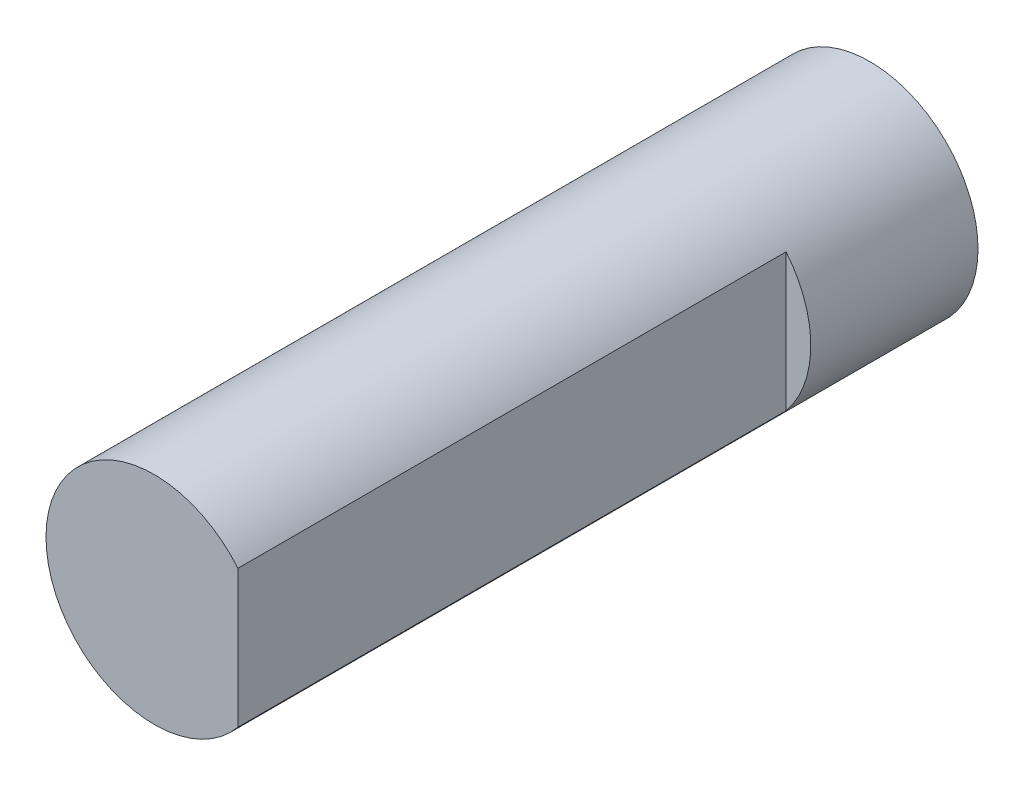
SolidWorks part; units mm, degrees
ref_plane "Front Plane" through (0, 0, 0) normal (0, 0, 1) x (1, 0, 0)
ref_plane "Top Plane" through (0, 0, 0) normal (0, 1, 0) x (1, 0, 0)
ref_plane "Right Plane" through (0, 0, 0) normal (1, 0, 0) x (0, 0, -1)
ref_plane "Plane1" through (0, 0, 54.6) normal (0, 0, 1) x (1, 0, 0)
sketch "Sketch17" plane through (0, 0, 54.6) normal (0, 0, 1) x (1, 0, 0)
  circle A0 centre (0, 0) radius 1.975
extrude "Boss-Extrude7" add sketch "Sketch17" along normal blind 13.05 contours A0
sketch "Sketch19" plane through (0, 0, 67.65) normal (0, 0, 1) x (1, 0, 0)
  line L0 (1.525, 0) -> (1.525, 1.255)
  line L1 (1.525, 0) -> (1.525, -1.255)
  line L2 (1.525, -1.255) -> (2.3539, -0.855)
  line L3 (2.3539, -0.855) -> (2.6616, 0.4191)
  line L4 (2.6616, 0.4191) -> (1.525, 1.255)
  circle A1 centre (0, 0) radius 1.975 construction
  dimension "D1" = 1.255
  dimension "D2" = 1.255
  dimension "D3" = 0
  dimension "D4" = 0
extrude "Cut-Extrude2" cut sketch "Sketch19" against normal blind 10
